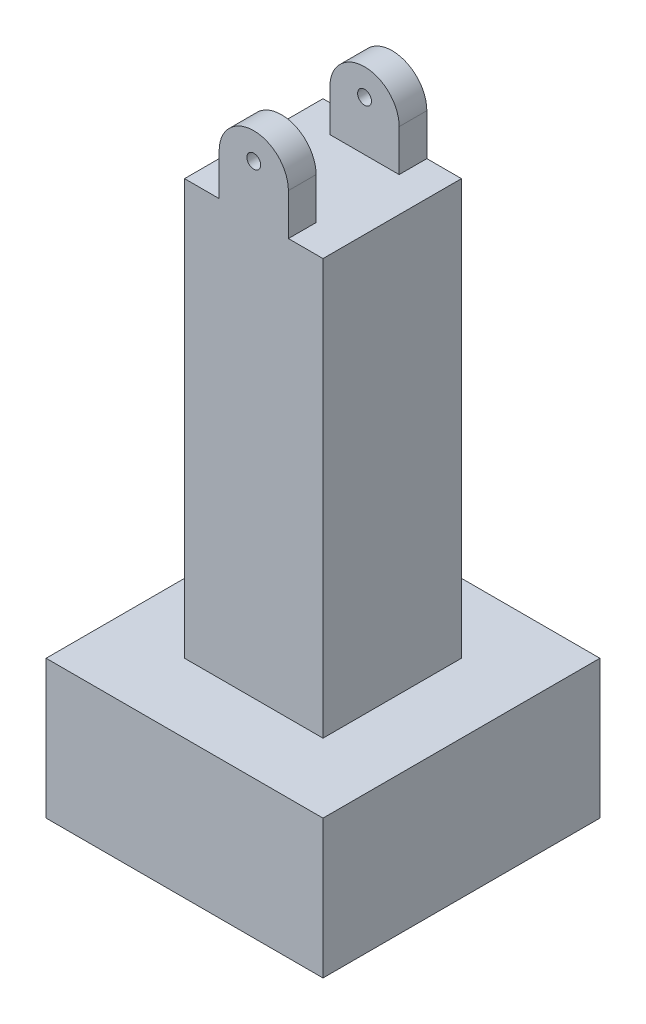
SolidWorks part; units mm, degrees
ref_plane "Front Plane" through (0, 0, 0) normal (0, 0, 1) x (1, 0, 0)
ref_plane "Top Plane" through (0, 0, 0) normal (0, 1, 0) x (1, 0, 0)
ref_plane "Right Plane" through (0, 0, 0) normal (1, 0, 0) x (0, 0, -1)
sketch "Sketch1" plane through (0, 0, 0) normal (0, 1, 0) x (1, 0, 0)
  line L1 (-10, 10) -> (10, 10)
  line L2 (-10, 10) -> (-10, -10)
  line L3 (-10, -10) -> (10, -10)
  line L4 (10, 10) -> (10, -10)
  line L5 (-10, 10) -> (10, -10) construction
  line L6 (-10, -10) -> (10, 10) construction
  point P0 (0, 0)
  dimension "D1" = 20
  dimension "D2" = 20
extrude "Boss-Extrude1" add sketch "Sketch1" along normal blind 10
sketch "Sketch2" plane through (0, 10, 0) normal (0, -1, 0) x (-1, 0, 0)
  line L1 (5, -5) -> (-5, -5)
  line L2 (5, -5) -> (5, 5)
  line L3 (5, 5) -> (-5, 5)
  line L4 (-5, -5) -> (-5, 5)
  line L5 (5, -5) -> (-5, 5) construction
  line L6 (5, 5) -> (-5, -5) construction
  point P0 (0, 0)
  dimension "D1" = 10
  dimension "D2" = 10
extrude "Boss-Extrude2" add sketch "Sketch2" against normal blind 30
sketch "Sketch3" plane through (0, 40, 0) normal (0, 1, 0) x (1, 0, 0)
  line L0 (5, 5) -> (5, -5) construction
  line L1 (2.5, 3) -> (-2.5, 3)
  line L2 (2.5, 3) -> (2.5, 5)
  line L3 (2.5, 5) -> (-2.5, 5)
  line L4 (-2.5, 3) -> (-2.5, 5)
  line L5 (2.5, 3) -> (-2.5, 5) construction
  line L6 (2.5, 5) -> (-2.5, 3) construction
  line L7 (-5, 5) -> (5, 5) construction
  line L9 (6.6353, 0) -> (-10.175, 0) construction
  line L10 (-2.5, -3) -> (-2.5, -5)
  line L11 (2.5, -5) -> (-2.5, -5)
  line L12 (2.5, -3) -> (2.5, -5)
  line L13 (2.5, -3) -> (-2.5, -3)
  point P0 (0, 4)
  dimension "D1" = 2
  dimension "D2" = 5
  dimension "D3" = 2.5
extrude "Boss-Extrude3" add sketch "Sketch3" along normal blind 3
sketch "Sketch4" plane through (0, 0, -5) normal (0, 0, -1) x (1, 0, 0)
  line L0 (2.5, -43) -> (-2.5, -43) construction
  line L1 (-2.5, -43) -> (-2.5, -40) construction
  circle A0 centre (0, -43) radius 2.5
extrude "Boss-Extrude4" add sketch "Sketch4" against normal blind 2
mirror "Mirror1" about plane through (0, 0, 0) normal (0, 0, 1) of "Boss-Extrude4"
sketch "Sketch5" plane through (0, 0, -5) normal (0, 0, -1) x (-1, 0, 0)
  circle A0 centre (0, 43.5892) radius 0.5
  dimension "D1" = 1
extrude "Cut-Extrude1" cut sketch "Sketch5" against normal blind 10
